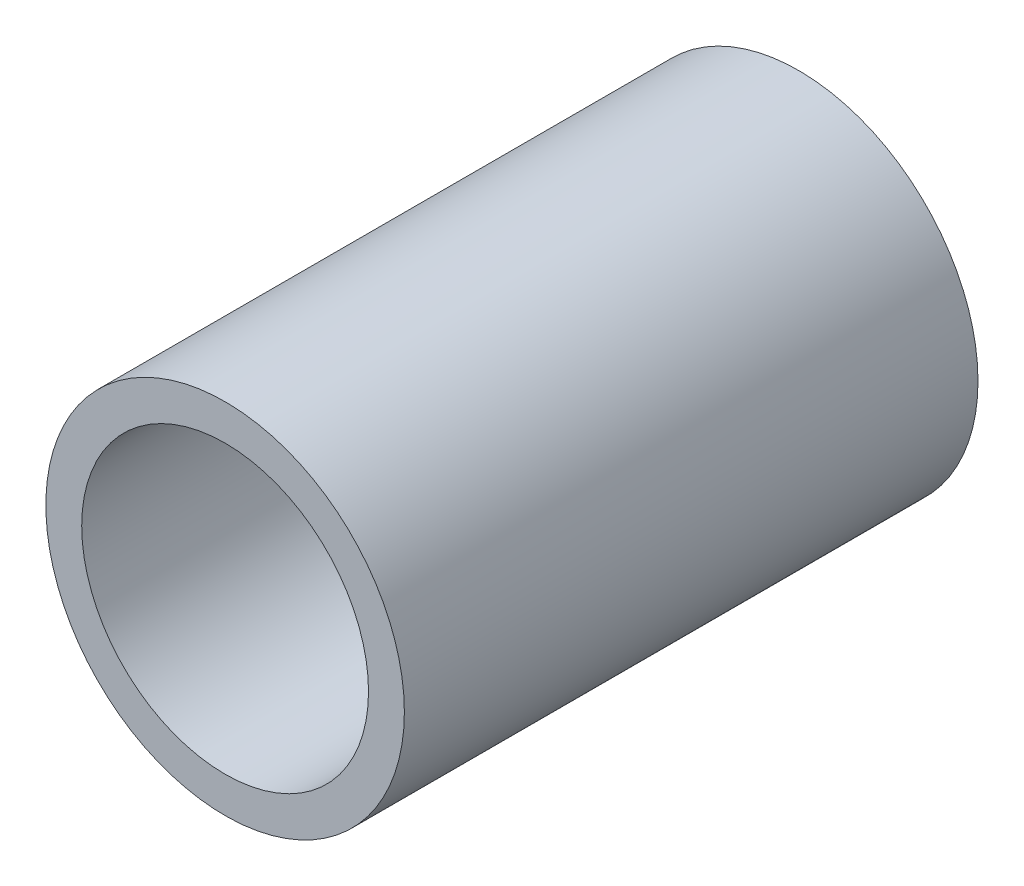
SolidWorks part; units mm, degrees
material "Polyetheretherketone (PEEK)"
ref_plane "Front Plane" through (0, 0, 0) normal (0, 0, 1) x (1, 0, 0)
ref_plane "Top Plane" through (0, 0, 0) normal (0, 1, 0) x (1, 0, 0)
ref_plane "Right Plane" through (0, 0, 0) normal (1, 0, 0) x (0, 0, -1)
sketch "Sketch1" plane through (0, 0, 0) normal (0, 0, 1) x (1, 0, 0)
  circle A0 centre (0, 0) radius 3.175
  circle A1 centre (0, 0) radius 3.9688
  dimension "D1" = 6.35
  dimension "D2" = 7.9375
extrude "Boss-Extrude1" add sketch "Sketch1" along normal blind 12.7
